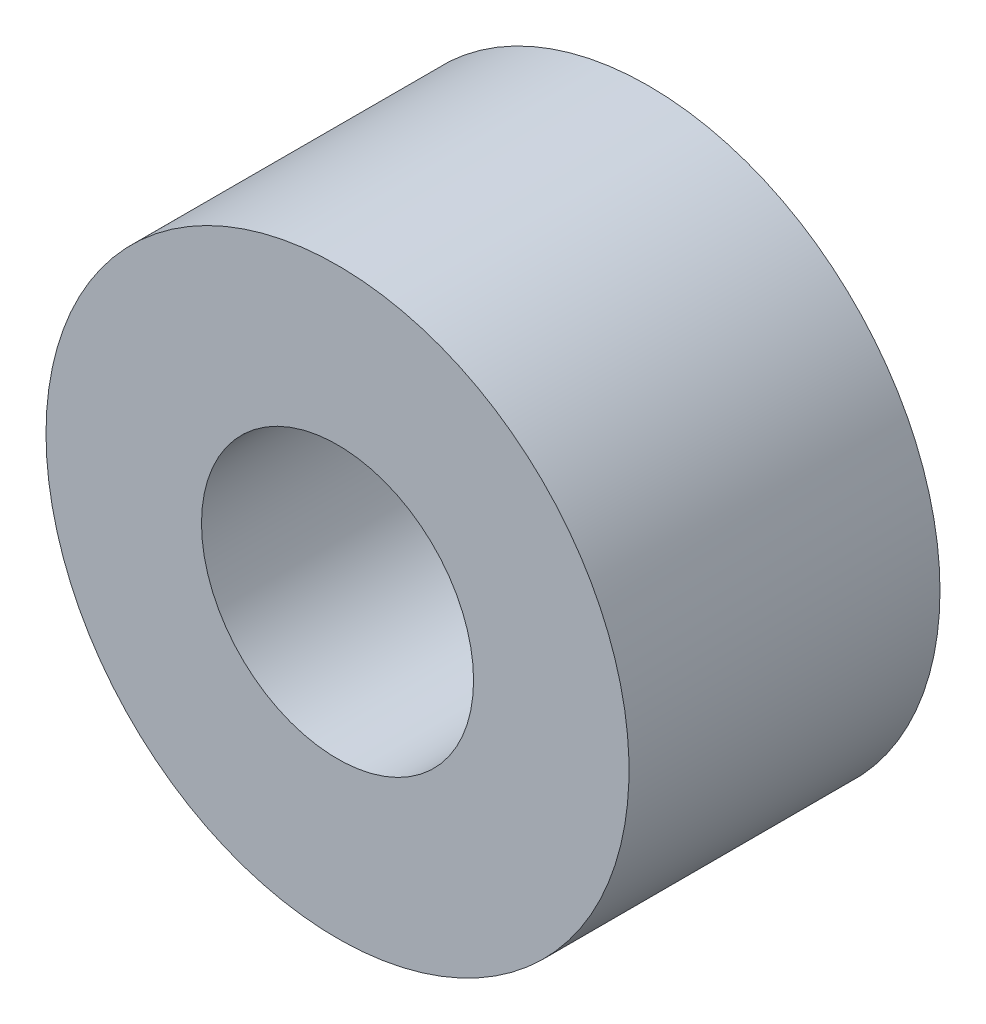
SolidWorks part; units mm, degrees
ref_plane "Спереди" through (0, 0, 0) normal (0, 0, 1) x (1, 0, 0)
ref_plane "Сверху" through (0, 0, 0) normal (0, 1, 0) x (1, 0, 0)
ref_plane "Справа" through (0, 0, 0) normal (1, 0, 0) x (0, 0, -1)
sketch "Эскиз1" plane through (0, 0, 0) normal (0, 0, 1) x (1, 0, 0)
  circle A0 centre (0, 5.8) radius 5.25 construction
  circle A1 centre (0, 5.8) radius 5.25
  circle A2 centre (0, 5.8) radius 11.25 construction
  circle A3 centre (0, 5.8) radius 11.25
extrude "Бобышка-Вытянуть1" add sketch "Эскиз1" along normal up to surface (12 mm away)
